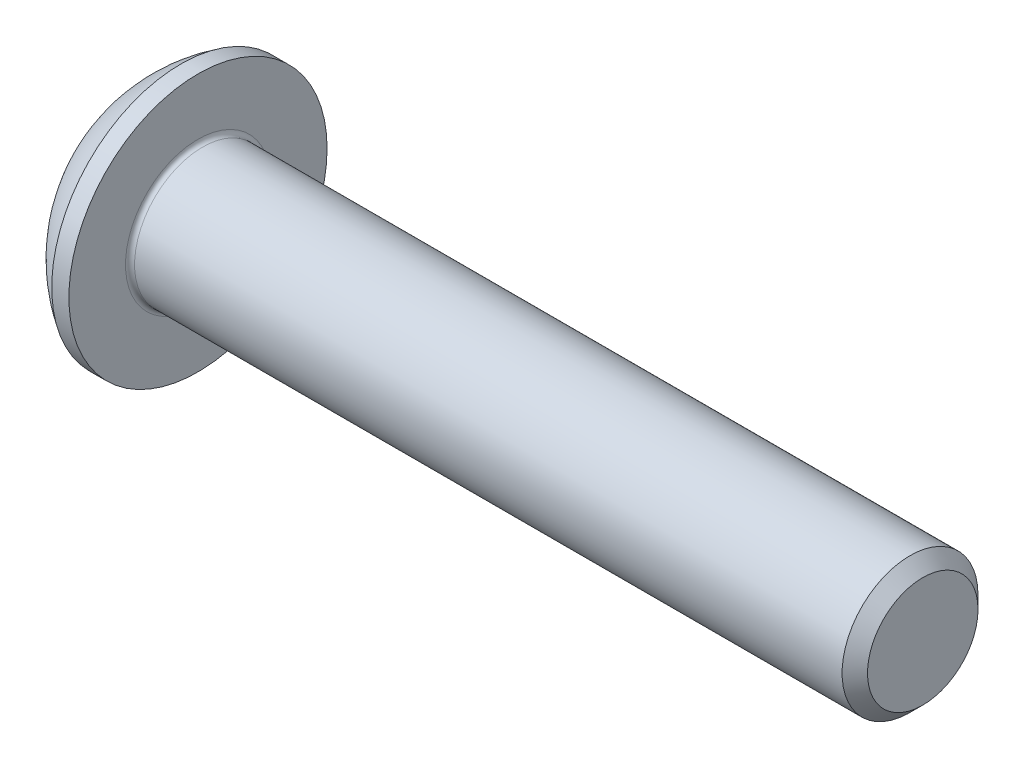
SolidWorks part; units mm, degrees
material "AISI 304"
ref_plane "Спереди" through (0, 0, 0) normal (0, 0, 1) x (1, 0, 0)
ref_plane "Сверху" through (0, 0, 0) normal (0, 1, 0) x (1, 0, 0)
ref_plane "Справа" through (0, 0, 0) normal (1, 0, 0) x (0, 0, -1)
sketch "Эскиз1" plane through (0, 0, 0) normal (0, 0, 1) x (1, 0, 0)
  line L0 (-3.6435, 0) -> (-10.508, 0) construction
  line L1 (0, 1.425) -> (0, 0)
  line L2 (0, 0) -> (17.65, 0)
  line L3 (17.65, 0) -> (17.65, 1.2195)
  line L4 (17.65, 1.2195) -> (17.3695, 1.5)
  line L5 (17.3695, 1.5) -> (1.65, 1.5)
  line L6 (1.65, 1.5) -> (1.65, 2.85)
  line L7 (1.65, 2.85) -> (1.2711, 2.85)
  arc A0 (1.2711, 2.85) -> (0, 1.425) centre (3.0318, 0) ccw
  dimension "D1" = 6.7
  dimension "D2" = 2.85
  dimension "D3" = 1.65
  dimension "D4" = 3
  dimension "D5" = 45
  dimension "D6" = 2.439
  dimension "D7" = 16
  dimension "D8" = 5.7
revolve "Body" add sketch "Эскиз1" angle 360 about L0
fillet "Скругление1" radius 0.1 1 edges at (1.65, 0, -1.5)
sketch "Эскиз2" plane through (0, 0, 0) normal (0, 0, 1) x (1, 0, 0)
  line L0 (0, 0) -> (0, 1)
  line L1 (0, 1.425) -> (0, -1.425) construction
  line L2 (0, 1) -> (1.04, 1)
  line L3 (1.04, 1) -> (1.6174, 0)
  line L4 (1.6174, 0) -> (0, 0)
  dimension "D1" = 1.04
  dimension "D2" = 60
  dimension "D3" = 1
revolve "Вырез-Повернуть1" cut sketch "Эскиз2" angle 360 about L4
sketch "Эскиз3" plane through (0, 0, 0) normal (-1, 0, 0) x (0, 0, 1)
  line L1 (-1, -0.5774) -> (0, -1.1547)
  line L2 (0, -1.1547) -> (1, -0.5774)
  line L3 (1, -0.5774) -> (1, 0.5774)
  line L4 (1, 0.5774) -> (0, 1.1547)
  line L5 (0, 1.1547) -> (-1, 0.5774)
  line L6 (-1, 0.5774) -> (-1, -0.5774)
  circle A0 centre (0, 0) radius 1 construction
  dimension "D1" = 2
extrude "Hex" cut sketch "Эскиз3" against normal blind 1.04
